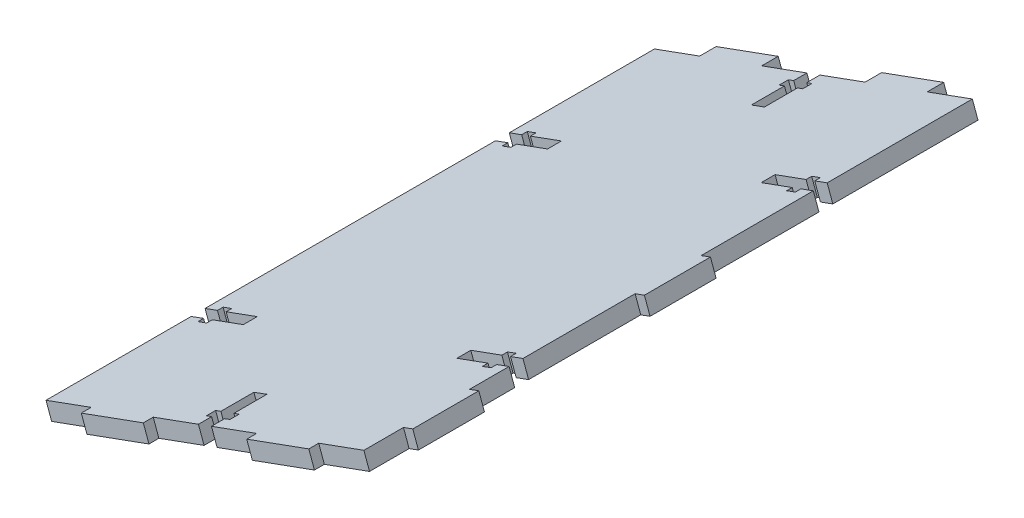
SolidWorks part; units mm, degrees
ref_plane "Front Plane" through (0, 0, 0) normal (0, 0, 1) x (1, 0, 0)
ref_plane "Top Plane" through (0, 0, 0) normal (0, 1, 0) x (1, 0, 0)
ref_plane "Right Plane" through (0, 0, 0) normal (1, 0, 0) x (0, 0, -1)
sketch "Sketch2" plane through (0, 0, 34.9) normal (0, 0, 1) x (1, 0, 0)
  line L12 (-76.8867, -45.5626) -> (-221.9898, -98.3304) construction
  line L17 (-52.9615, -36.8621) -> (-51.2527, -41.561)
  line L18 (-52.9615, -36.8621) -> (-149.2503, -71.8781)
  line L19 (-51.2527, -41.561) -> (-147.5415, -76.5771)
  line L20 (-149.2503, -71.8781) -> (-147.5415, -76.5771)
  line L24 (-138.6762, -100.9552) -> (-127.3981, -131.9681) construction
  dimension "D1" = 5
extrude "Boss-Extrude1" add sketch "Sketch2" along normal up to surface (184.3 mm away)
sketch "Sketch4" plane through (7.3623, -20.2452, 0) normal (0.3418, -0.9398, 0) x (-0.9398, -0.3418, 0)
  line L0 (111.4996, -34.9) -> (115.6996, -34.9)
  line L1 (111.4996, -34.9) -> (111.4996, -38.9)
  line L2 (115.6996, -34.9) -> (115.6996, -38.9)
  line L3 (109.7996, -38.9) -> (111.4996, -38.9)
  line L4 (109.7996, -38.9) -> (109.7996, -41.7)
  line L5 (117.3996, -38.9) -> (117.3996, -41.7)
  line L6 (109.7996, -41.7) -> (111.4996, -41.7)
  line L7 (111.4996, -41.7) -> (111.4996, -51.7)
  line L8 (115.6996, -41.7) -> (115.6996, -51.7)
  line L9 (111.4996, -51.7) -> (115.6996, -51.7)
  line L10 (115.6996, -41.7) -> (117.3996, -41.7)
  line L11 (115.6996, -38.9) -> (117.3996, -38.9)
  line L14 (62.3706, -83.075) -> (62.3706, -78.875)
  line L25 (62.3706, -34.9) -> (164.8286, -34.9) construction
  line L26 (115.6996, -219.2) -> (111.4996, -219.2)
  line L27 (115.6996, -219.2) -> (115.6996, -215.2)
  line L28 (113.5996, -51.7) -> (113.5996, -34.9) construction
  line L29 (111.4996, -219.2) -> (111.4996, -215.2)
  line L30 (117.3996, -215.2) -> (115.6996, -215.2)
  line L31 (117.3996, -215.2) -> (117.3996, -212.4)
  line L32 (109.7996, -215.2) -> (109.7996, -212.4)
  line L33 (117.3996, -212.4) -> (115.6996, -212.4)
  line L34 (115.6996, -212.4) -> (115.6996, -202.4)
  line L35 (111.4996, -212.4) -> (111.4996, -202.4)
  line L36 (115.6996, -202.4) -> (111.4996, -202.4)
  line L37 (111.4996, -212.4) -> (109.7996, -212.4)
  line L38 (111.4996, -215.2) -> (109.7996, -215.2)
  line L39 (113.5996, -202.4) -> (113.5996, -219.2) construction
  line L40 (62.3706, -219.2) -> (164.8286, -219.2) construction
  line L41 (62.3706, -83.075) -> (66.3706, -83.075)
  line L42 (62.3706, -78.875) -> (66.3706, -78.875)
  line L43 (66.3706, -84.775) -> (66.3706, -83.075)
  line L44 (66.3706, -84.775) -> (69.1706, -84.775)
  line L45 (66.3706, -77.175) -> (69.1706, -77.175)
  line L46 (69.1706, -84.775) -> (69.1706, -83.075)
  line L47 (69.1706, -83.075) -> (79.1706, -83.075)
  line L48 (69.1706, -78.875) -> (79.1706, -78.875)
  line L49 (79.1706, -83.075) -> (79.1706, -78.875)
  line L50 (69.1706, -78.875) -> (69.1706, -77.175)
  line L51 (66.3706, -78.875) -> (66.3706, -77.175)
  line L52 (79.1706, -80.975) -> (62.3706, -80.975) construction
  line L55 (62.3706, -219.2) -> (62.3706, -34.9) construction
  line L56 (62.3706, -34.9) -> (62.3706, -127.05) construction
  line L57 (62.3706, -127.05) -> (164.8286, -127.05) construction
  line L58 (79.1706, -173.125) -> (62.3706, -173.125) construction
  line L59 (66.3706, -175.225) -> (66.3706, -176.925)
  line L60 (69.1706, -175.225) -> (69.1706, -176.925)
  line L61 (79.1706, -171.025) -> (79.1706, -175.225)
  line L62 (69.1706, -175.225) -> (79.1706, -175.225)
  line L63 (69.1706, -171.025) -> (79.1706, -171.025)
  line L64 (69.1706, -169.325) -> (69.1706, -171.025)
  line L65 (66.3706, -176.925) -> (69.1706, -176.925)
  line L66 (66.3706, -169.325) -> (69.1706, -169.325)
  line L67 (66.3706, -169.325) -> (66.3706, -171.025)
  line L68 (62.3706, -175.225) -> (66.3706, -175.225)
  line L69 (62.3706, -171.025) -> (66.3706, -171.025)
  line L70 (62.3706, -171.025) -> (62.3706, -175.225)
  line L76 (164.8286, -219.2) -> (164.8286, -34.9) construction
  line L77 (113.5996, -171.4513) -> (113.5996, -40.1199) construction
  line L78 (148.0286, -173.125) -> (164.8286, -173.125) construction
  line L87 (164.8286, -34.9) -> (164.8286, -127.05) construction
  line L88 (148.0286, -80.975) -> (164.8286, -80.975) construction
  line L89 (164.8286, -171.025) -> (164.8286, -175.225)
  line L90 (164.8286, -171.025) -> (160.8286, -171.025)
  line L91 (164.8286, -175.225) -> (160.8286, -175.225)
  line L92 (160.8286, -169.325) -> (160.8286, -171.025)
  line L93 (160.8286, -169.325) -> (158.0286, -169.325)
  line L94 (160.8286, -176.925) -> (158.0286, -176.925)
  line L95 (158.0286, -169.325) -> (158.0286, -171.025)
  line L96 (158.0286, -171.025) -> (148.0286, -171.025)
  line L97 (158.0286, -175.225) -> (148.0286, -175.225)
  line L98 (148.0286, -171.025) -> (148.0286, -175.225)
  line L99 (158.0286, -175.225) -> (158.0286, -176.925)
  line L100 (160.8286, -175.225) -> (160.8286, -176.925)
  line L101 (160.8286, -78.875) -> (160.8286, -77.175)
  line L102 (158.0286, -78.875) -> (158.0286, -77.175)
  line L103 (148.0286, -83.075) -> (148.0286, -78.875)
  line L104 (158.0286, -78.875) -> (148.0286, -78.875)
  line L105 (158.0286, -83.075) -> (148.0286, -83.075)
  line L106 (158.0286, -84.775) -> (158.0286, -83.075)
  line L107 (160.8286, -77.175) -> (158.0286, -77.175)
  line L108 (160.8286, -84.775) -> (158.0286, -84.775)
  line L109 (160.8286, -84.775) -> (160.8286, -83.075)
  line L110 (164.8286, -78.875) -> (160.8286, -78.875)
  line L111 (164.8286, -83.075) -> (160.8286, -83.075)
  line L112 (164.8286, -83.075) -> (164.8286, -78.875)
  point P70 (113.5996, -127.05)
  dimension "D1" = 4.2
  dimension "D2" = 1.7
  dimension "D3" = 1.7
  dimension "D4" = 2.8
  dimension "D5" = 10
  dimension "D6" = 4
  dimension "D7" = 4.2
  dimension "D8" = 1.7
  dimension "D9" = 1.7
  dimension "D10" = 2.8
  dimension "D11" = 10
  dimension "D12" = 4
  dimension "D13" = 4.2
  dimension "D14" = 1.7
  dimension "D15" = 1.7
  dimension "D16" = 2.8
  dimension "D17" = 10
  dimension "D18" = 4
extrude "Cut-Extrude3" cut sketch "Sketch4" against normal through all
sketch "Sketch5" plane through (7.3623, -20.2452, 0) normal (0.3418, -0.9398, 0) x (0.9398, 0.3418, 0)
  line L0 (-130.2641, 219.2) -> (-150.2641, 219.2)
  line L1 (-130.2641, 219.2) -> (-130.2641, 222.2)
  line L2 (-150.2641, 219.2) -> (-150.2641, 222.2)
  line L3 (-130.2641, 222.2) -> (-150.2641, 222.2)
  line L4 (-164.8286, 219.2) -> (-115.6996, 219.2) construction
  line L5 (-76.9351, 219.2) -> (-96.9351, 219.2)
  line L6 (-76.9351, 219.2) -> (-76.9351, 222.2)
  line L7 (-96.9351, 219.2) -> (-96.9351, 222.2)
  line L8 (-76.9351, 222.2) -> (-96.9351, 222.2)
  line L9 (-111.4996, 219.2) -> (-62.3706, 219.2) construction
  line L10 (-62.3706, 117.05) -> (-62.3706, 137.05)
  line L11 (-62.3706, 117.05) -> (-59.3706, 117.05)
  line L12 (-62.3706, 137.05) -> (-59.3706, 137.05)
  line L13 (-59.3706, 117.05) -> (-59.3706, 137.05)
  line L14 (-62.3706, 83.075) -> (-62.3706, 171.025) construction
  line L15 (-62.3706, 207.2125) -> (-62.3706, 187.2125)
  line L16 (-62.3706, 207.2125) -> (-59.3706, 207.2125)
  line L17 (-62.3706, 187.2125) -> (-59.3706, 187.2125)
  line L18 (-59.3706, 207.2125) -> (-59.3706, 187.2125)
  line L19 (-62.3706, 175.225) -> (-62.3706, 219.2) construction
  line L20 (-62.3706, 92.4) -> (-62.3706, 161.7)
  line L24 (-62.3706, 83.075) -> (-62.3706, 171.025) construction
  line L25 (-150.2641, 34.9) -> (-130.2641, 34.9)
  line L26 (-150.2641, 34.9) -> (-150.2641, 29.9)
  line L27 (-130.2641, 34.9) -> (-130.2641, 29.9)
  line L28 (-150.2641, 29.9) -> (-130.2641, 29.9)
  line L29 (-164.8286, 34.9) -> (-115.6996, 34.9) construction
  line L30 (-96.9351, 34.9) -> (-76.9351, 34.9)
  line L31 (-96.9351, 34.9) -> (-96.9351, 29.9)
  line L32 (-76.9351, 34.9) -> (-76.9351, 29.9)
  line L33 (-96.9351, 29.9) -> (-76.9351, 29.9)
  line L34 (-111.4996, 34.9) -> (-62.3706, 34.9) construction
  line L35 (25.1714, 222.2) -> (-242.2286, 222.2) construction
  point P10 (-140.2641, 219.2)
  point P11 (-86.9351, 219.2)
  point P16 (-62.3706, 127.05)
  point P23 (-62.3706, 197.2125)
  point P31 (-62.3706, 127.05)
  point P39 (-140.2641, 34.9)
  point P49 (-86.9351, 34.9)
  dimension "D2" = 20
  dimension "D4" = 20
  dimension "D5" = 3
  dimension "D6" = 20
  dimension "D7" = 3
  dimension "D8" = 20
  dimension "D11" = 5
  dimension "D12" = 20
  dimension "D13" = 5
  dimension "D14" = 20
extrude "Boss-Extrude2" add sketch "Sketch5" against normal blind 5 contours L31 L33 L32 L30 | L26 L28 L27 L25 | L11 L13 L12 L10 | L18 L16 L15 L17 | L6 L8 L7 L5 | L1 L3 L2 L0
